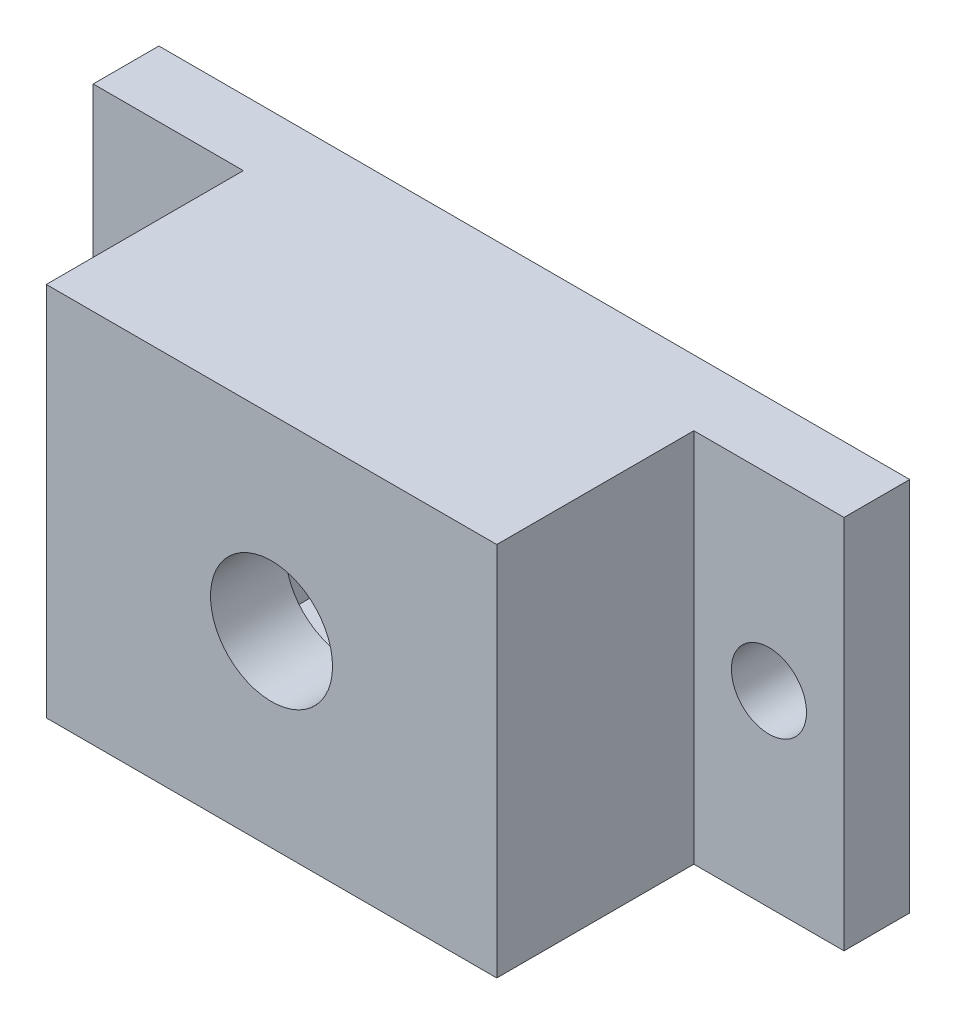
SolidWorks part; units mm, degrees
ref_plane "Front Plane" through (0, 0, 0) normal (0, 0, 1) x (1, 0, 0)
ref_plane "Top Plane" through (0, 0, 0) normal (0, 1, 0) x (1, 0, 0)
ref_plane "Right Plane" through (0, 0, 0) normal (1, 0, 0) x (0, 0, -1)
sketch "Sketch2" plane through (0, 0, 0) normal (0, 0, 1) x (1, 0, 0)
  line L0 (-61.2001, 6.4093) -> (-21.2001, 6.4093) construction
  line L1 (-61.2001, 16.4093) -> (-21.2001, 16.4093)
  line L2 (-61.2001, 16.4093) -> (-61.2001, -3.5907)
  line L3 (-61.2001, -3.5907) -> (-21.2001, -3.5907)
  line L4 (-21.2001, 16.4093) -> (-21.2001, -3.5907)
  line L5 (-41.2001, 16.4093) -> (-41.2001, -3.5907) construction
  line L6 (-57.2001, 6.4093) -> (-25.2001, 6.4093) construction
  circle A0 centre (-57.2001, 6.4093) radius 2
  circle A1 centre (-25.2001, 6.4093) radius 2
  point P12 (-41.2001, 6.4093)
  point P13 (-41.2001, 6.4093)
  point P14 (0, 0)
  dimension "D3" = 4
  dimension "D4" = 4
  dimension "D1" = 20
  dimension "D2" = 40
  dimension "D5" = 32
extrude "Boss-Extrude1" add sketch "Sketch2" along normal blind 3.5
sketch "Sketch3" plane through (0, 0, 3.5) normal (0, 0, 1) x (1, 0, 0)
  line L0 (-61.2001, -3.5907) -> (-21.2001, -3.5907) construction
  line L1 (-53.2001, -3.5907) -> (-29.2001, -3.5907)
  line L2 (-53.2001, -3.5907) -> (-53.2001, 16.4093)
  line L3 (-53.2001, 16.4093) -> (-29.2001, 16.4093)
  line L4 (-29.2001, -3.5907) -> (-29.2001, 16.4093)
  line L5 (-21.2001, 16.4093) -> (-61.2001, 16.4093) construction
  line L6 (-61.2001, 16.4093) -> (-61.2001, -3.5907) construction
  dimension "D1" = 24
  dimension "D2" = 8
extrude "Boss-Extrude2" add sketch "Sketch3" along normal blind 10.5
sketch "Sketch4" plane through (0, 0, 0) normal (0, 0, -1) x (-1, 0, 0)
  line L1 (50.2001, 14.9093) -> (32.2001, 14.9093)
  line L2 (50.2001, 14.9093) -> (50.2001, -2.0907)
  line L3 (50.2001, -2.0907) -> (32.2001, -2.0907)
  line L4 (32.2001, 14.9093) -> (32.2001, -2.0907)
  line L6 (61.2001, 16.4093) -> (61.2001, -3.5907) construction
  line L7 (21.2001, 16.4093) -> (61.2001, 16.4093) construction
  line L8 (61.2001, -3.5907) -> (21.2001, -3.5907) construction
  dimension "D1" = 18
  dimension "D2" = 11
  dimension "D3" = 1.5
  dimension "D4" = 1.5
extrude "Cut-Extrude2" cut sketch "Sketch4" against normal blind 10
sketch "Sketch5" plane through (0, 0, 14) normal (0, 0, 1) x (1, 0, 0)
  line L0 (-53.2001, 6.4093) -> (-29.2001, 6.4093) construction
  line L1 (-53.2001, 16.4093) -> (-53.2001, -3.5907) construction
  line L2 (-29.2001, -3.5907) -> (-29.2001, 16.4093) construction
  line L3 (-41.2001, 16.4093) -> (-41.2001, -3.5907) construction
  line L4 (-29.2001, 16.4093) -> (-53.2001, 16.4093) construction
  line L5 (-53.2001, -3.5907) -> (-29.2001, -3.5907) construction
  circle A0 centre (-41.2001, 6.4093) radius 3.25
  dimension "D1" = 6.5
extrude "Cut-Extrude3" cut sketch "Sketch5" against normal through all
